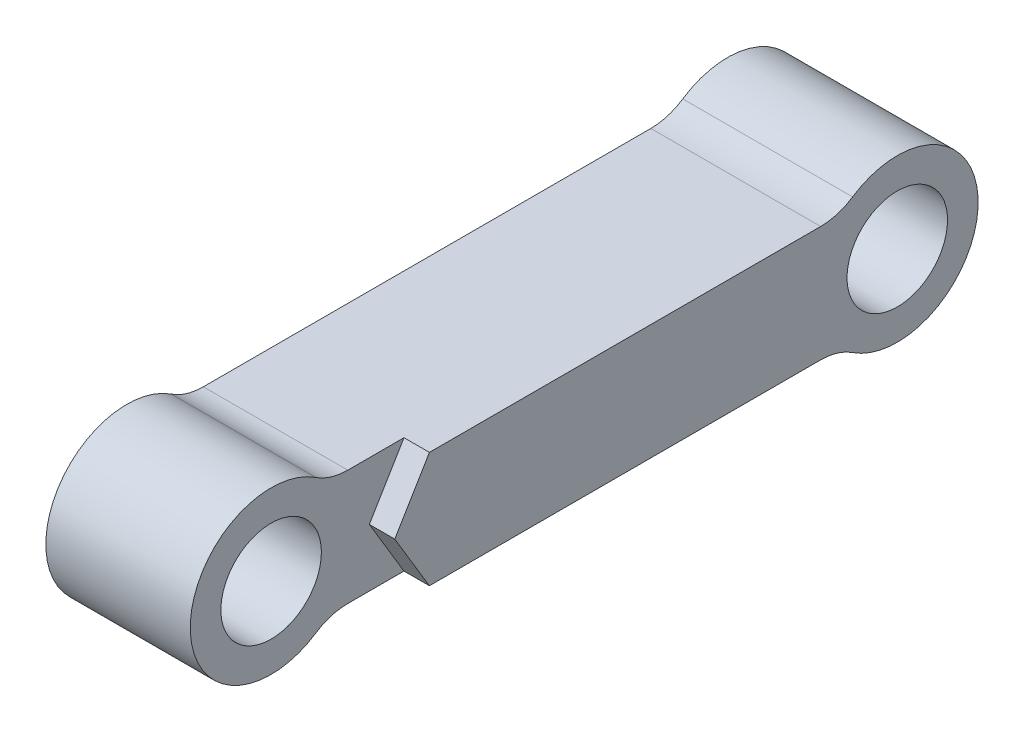
SolidWorks part; units mm, degrees
ref_plane "Alzado" through (0, 0, 0) normal (0, 0, 1) x (1, 0, 0)
ref_plane "Planta" through (0, 0, 0) normal (0, 1, 0) x (1, 0, 0)
ref_plane "Vista lateral" through (0, 0, 0) normal (1, 0, 0) x (0, 0, -1)
sketch "Croquis1" plane through (0, 0, 0) normal (1, 0, 0) x (0, 0, -1)
  line L0 (-26, 0) -> (26, 0) construction
  line L1 (-19.3668, 5) -> (19.3668, 5)
  line L2 (-19.3668, -5) -> (19.3668, -5)
  arc A0 (-22.1306, 5.8333) -> (-22.1306, -5.8333) centre (-26, 0) ccw
  circle A1 centre (-26, 0) radius 4.35
  arc A2 (22.1306, -5.8333) -> (22.1306, 5.8333) centre (26, 0) ccw
  circle A3 centre (26, 0) radius 4.35
  arc A4 (-22.1306, 5.8333) -> (-19.1927, 5.003) centre (-19.3668, 10) ccw
  arc A5 (-22.1306, -5.8333) -> (-19.3668, -5) centre (-19.3668, -10) cw
  arc A6 (19.3668, -5) -> (22.1306, -5.8333) centre (19.3668, -10) cw
  arc A7 (19.3668, 5) -> (22.1306, 5.8333) centre (19.3668, 10) ccw
  point P2 (0, 0)
  point P8 (0, 5)
  dimension "D2" = 8.7
  dimension "D3" = 14
  dimension "D5" = 5
  dimension "D6" = 5
  dimension "D7" = 5
  dimension "D8" = 5
  dimension "D1" = 52
  dimension "D4" = 5
extrude "Saliente-Extruir1" add sketch "Croquis1" along normal blind 14.7
sketch "Croquis2" plane through (14.7, 0, 0) normal (1, 0, 0) x (0, 0, -1)
  line L0 (-33, 0) -> (-17.5, 0) construction
  line L1 (-14.5, 5) -> (-14.5, -5)
  line L2 (-19.3668, 5) -> (19.3668, 5) construction
  line L3 (-14.5, 5) -> (-17.5, 0)
  line L4 (-17.5, 0) -> (-14.5, -5)
  line L5 (-19.3668, 5) -> (-23.5579, 6.5602)
  line L6 (-19.3668, -5) -> (-14.5, -5)
  line L7 (-19.3668, -5) -> (-23.5579, -6.5602)
  line L8 (-19.3668, 5) -> (-14.5, 5)
  arc A0 (-22.1306, 5.8333) -> (-22.1306, -5.8333) centre (-26, 0) ccw construction
  circle A1 centre (-26, 0) radius 7
  point P5 (-33, 0)
  point P8 (-14.5, 0)
  dimension "D3" = 14
  dimension "D1" = 15.5
  dimension "D2" = 18.5
extrude "Cortar-Extruir1" cut sketch "Croquis2" against normal blind 2.2
